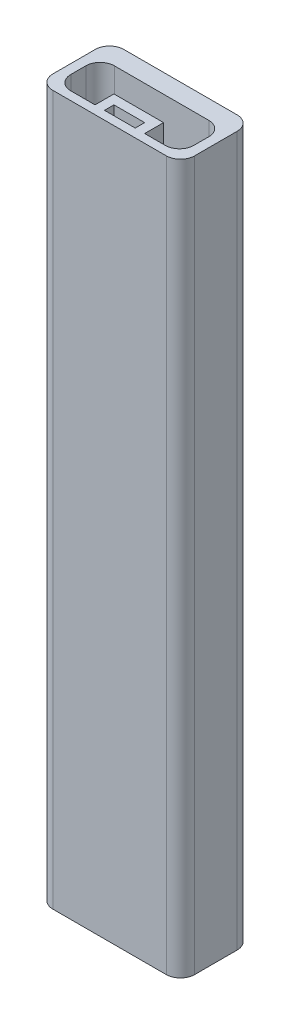
SolidWorks part; units mm, degrees
ref_plane "Front Plane" through (0, 0, 0) normal (0, 0, 1) x (1, 0, 0)
ref_plane "Top Plane" through (0, 0, 0) normal (0, 1, 0) x (1, 0, 0)
ref_plane "Right Plane" through (0, 0, 0) normal (1, 0, 0) x (0, 0, -1)
sketch "Sketch2" plane through (0, 0, 0) normal (0, 1, 0) x (1, 0, 0)
  line L0 (-55, 0) -> (55, 0) construction
  line L1 (-15, 7.5) -> (15, 7.5)
  line L2 (-15, 7.5) -> (-15, -7.5)
  line L3 (-15, -7.5) -> (15, -7.5)
  line L4 (15, 7.5) -> (15, -7.5)
  line L5 (0, -55) -> (0, 55) construction
  line L7 (-13, 3.5) -> (13, 3.5)
  line L8 (-13, 3.5) -> (-13, -5.7)
  line L9 (-13, -5.7) -> (13, -5.7)
  line L10 (13, 3.5) -> (13, -5.7)
  dimension "D1" = 30
  dimension "D2" = 15
  dimension "D3" = 7.5
  dimension "D4" = 15
  dimension "D5" = 2
  dimension "D6" = 2
  dimension "D7" = 4
  dimension "D8" = 1.8
extrude "Boss-Extrude1" add sketch "Sketch2" along normal blind 150
sketch "Sketch3" plane through (0, 150, 0) normal (0, 1, 0) x (1, 0, 0)
  line L0 (-2.8716, -5.7) -> (-2.8716, -3.7)
  line L1 (-13, -5.7) -> (13, -5.7) construction
  line L2 (-2.8716, -3.7) -> (3.6315, -3.7)
  line L3 (3.6315, -3.7) -> (3.6315, -5.7)
  line L4 (3.6315, -5.7) -> (5.6315, -5.7)
  line L5 (5.6315, -5.7) -> (5.6315, -1.7)
  line L6 (5.6315, -1.7) -> (-4.8716, -1.7)
  line L7 (-4.8716, -1.7) -> (-4.8716, -5.7)
  line L8 (-4.8716, -5.7) -> (-2.8716, -5.7)
  dimension "D1" = 2
  dimension "D2" = 2
  dimension "D3" = 4
  dimension "D4" = 2
extrude "Boss-Extrude2" add sketch "Sketch3" against normal blind 5
fillet "Fillet1" radius 3 8 edges at (13, 75, 5.7) (13, 75, -3.5) (-13, 75, 5.7) (-13, 75, -3.5) (-15, 75, 7.5) (-15, 75, -7.5) (15, 75, 7.5) (15, 75, -7.5)
pattern_linear "LPattern1" count 15 spacing 10 along (0, -1, 0) of "Boss-Extrude2"
